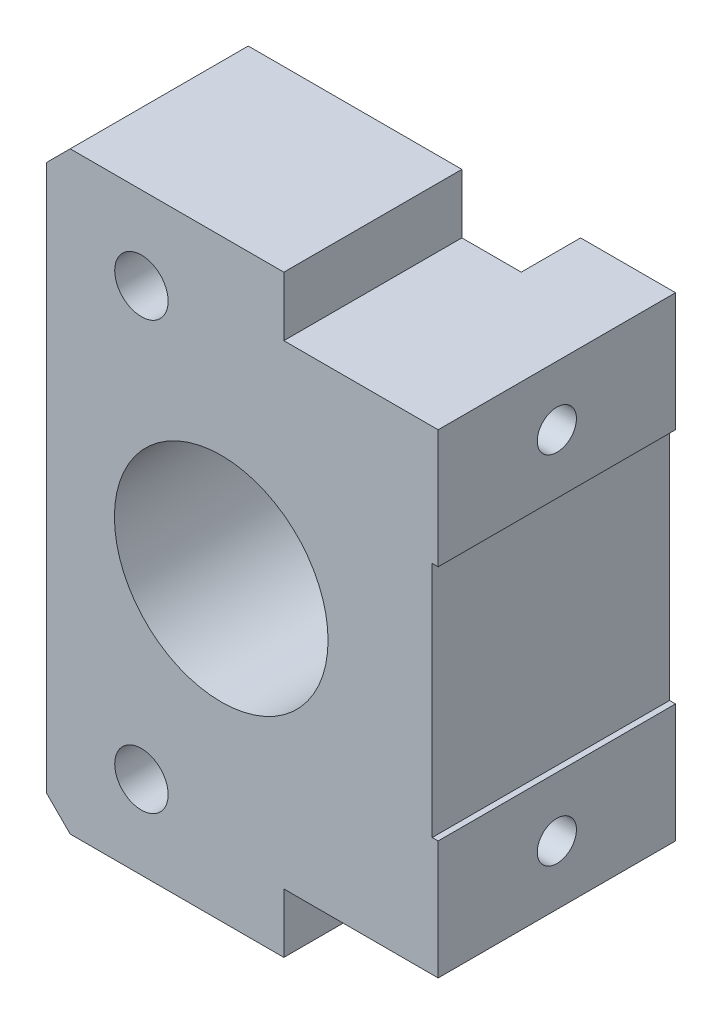
SolidWorks part; units mm, degrees
ref_plane "Front Plane" through (0, 0, 0) normal (0, 0, 1) x (1, 0, 0)
ref_plane "Top Plane" through (0, 0, 0) normal (0, 1, 0) x (1, 0, 0)
ref_plane "Right Plane" through (0, 0, 0) normal (1, 0, 0) x (0, 0, -1)
sketch "Sketch4" plane through (0, 0, 0) normal (0, 0, 1) x (1, 0, 0)
  line L0 (-38.3333, -25.2778) -> (-38.3333, 24.7222)
  line L1 (-38.3333, 24.7222) -> (-18.3333, 24.7222)
  line L2 (-18.3333, 24.7222) -> (-18.3333, 19.7222)
  line L3 (-18.3333, 19.7222) -> (-5.3333, 19.7222)
  line L4 (-5.3333, 19.7222) -> (-5.3333, 9.7222)
  line L5 (-5.3333, 9.7222) -> (-5.8333, 9.7222)
  line L6 (-5.8333, 9.7222) -> (-5.8333, -10.2778)
  line L7 (-5.8333, -10.2778) -> (-5.3333, -10.2778)
  line L8 (-5.3333, -10.2778) -> (-5.3333, -20.2778)
  line L9 (-18.3333, -25.2778) -> (-38.3333, -25.2778)
  line L10 (-5.3333, -20.2778) -> (-18.3333, -20.2778)
  line L11 (-18.3333, -20.2778) -> (-18.3333, -25.2778)
  circle A0 centre (-23.6085, -0.2778) radius 9
  dimension "D10" = 18
  dimension "D1" = 50
  dimension "D2" = 13
  dimension "D3" = 20
  dimension "D4" = 20
  dimension "D5" = 5
  dimension "D6" = 5
  dimension "D7" = 10
  dimension "D8" = 10
  dimension "D9" = 0.5
extrude "Boss-Extrude1" add sketch "Sketch4" along normal blind 15
sketch "Sketch5" plane through (0, 0, 0) normal (0, 0, -1) x (-1, 0, 0)
  line L0 (38.3333, 24.7222) -> (38.3333, -25.2778) construction
  line L1 (18.3333, 24.7222) -> (38.3333, 24.7222) construction
  line L2 (38.3333, -25.2778) -> (18.3333, -25.2778) construction
  circle A0 centre (30.3333, 17.7222) radius 4
  circle A1 centre (30.3333, -18.2778) radius 4
  point P4 (0, 0)
  dimension "D1" = 8
  dimension "D2" = 8
  dimension "D3" = 7
  dimension "D4" = 7
extrude "Cut-Extrude1" cut sketch "Sketch5" against normal blind 7
sketch "Sketch6" plane through (0, 0, 7) normal (0, 0, -1) x (-1, 0, 0)
  circle A0 centre (30.3333, 17.7222) radius 2.25
  circle A1 centre (30.3333, -18.2778) radius 2.25
  dimension "D1" = 4.5
extrude "Cut-Extrude2" cut sketch "Sketch6" against normal through all
sketch "Sketch9" plane through (0, 0, 0) normal (0, 0, -1) x (-1, 0, 0)
  line L0 (13.3333, -20.2778) -> (5.3333, -20.2778)
  line L1 (18.3333, -20.2778) -> (5.3333, -20.2778) construction
  line L2 (5.3333, -20.2778) -> (5.3333, -10.2778)
  line L3 (5.3333, -10.2778) -> (5.8333, -10.2778)
  line L4 (5.8333, -10.2778) -> (5.8333, 9.7222)
  line L5 (5.8333, 9.7222) -> (5.3333, 9.7222)
  line L6 (5.3333, 9.7222) -> (5.3333, 19.7222)
  line L7 (5.3333, 9.7222) -> (5.3333, 19.7222) construction
  line L8 (5.3333, 19.7222) -> (13.3333, 19.7222)
  line L9 (5.3333, 19.7222) -> (18.3333, 19.7222) construction
  line L10 (13.3333, 19.7222) -> (13.3333, -20.2778)
  dimension "D1" = 8
extrude "Boss-Extrude3" add sketch "Sketch9" along normal blind 5
chamfer "Chamfer1" distance 2 angle 45 2 edges at (-38.3333, 24.7222, 7.5) (-38.3333, -25.2778, 7.5)
hole_wizard "M4 Tapped Hole1" positions "Sketch10" profile "Sketch11" tap size "M4" standard "ISO"
sketch "Sketch10" plane through (-5.3333, 0, 0) normal (1, 0, 0) x (0, 0, -1)
  line L0 (-15, -25.2778) -> (0, -25.2778) construction
  line L1 (-15, 19.7222) -> (-15, 24.7222) construction
  point P0 (-5, 14.7222)
  point P2 (-5, -15.2778)
  dimension "D1" = 40
  dimension "D2" = 10
  dimension "D3" = 10
sketch "Sketch11" plane through (-5.3333, 14.7222, 5) normal (0, 1, 0) x (0, 0, -1)
  line L0 (0, 0) -> (0, 8.9914)
  line L1 (0, 8.9914) -> (1.65, 8)
  line L2 (1.65, 8) -> (1.65, 0)
  line L5 (1.65, 0) -> (0, 0)
  line L10 (0, 8.9914) -> (-1.65, 8) construction
  line L11 (0, -6.35) -> (0, 107.95) construction
  dimension "Tap Drill Dia." = 3.3
  dimension "Tap Drill Depth" = 8
  dimension "Drill Angle" = 118
cosmetic thread "Hole Thread1" parameters "D1"=8, "D2"=4
cosmetic thread "Hole Thread2" parameters "D1"=8, "D2"=4
